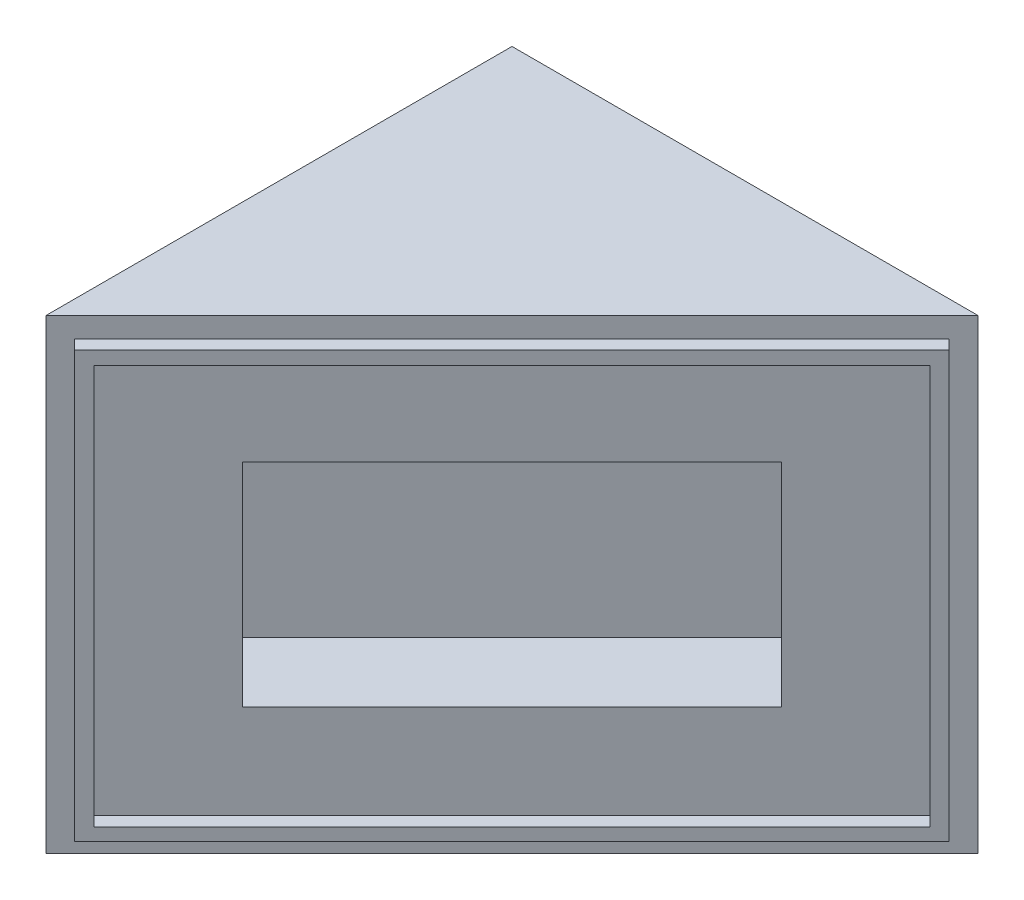
SolidWorks part; units mm, degrees
ref_plane "Front Plane" through (0, 0, 0) normal (0, 0, 1) x (1, 0, 0)
ref_plane "Top Plane" through (0, 0, 0) normal (0, 1, 0) x (1, 0, 0)
ref_plane "Right Plane" through (0, 0, 0) normal (1, 0, 0) x (0, 0, -1)
sketch "Sketch1" plane through (0, 0, 0) normal (0, 1, 0) x (1, 0, 0)
  line L1 (0, 0) -> (69.85, 0)
  line L2 (0, 0) -> (0, 69.85)
  line L3 (0, 69.85) -> (69.85, 69.85)
  line L4 (69.85, 0) -> (69.85, 69.85)
  dimension "D1" = 69.85
  dimension "D2" = 69.85
extrude "Boss-Extrude1" add sketch "Sketch1" along normal blind 69.85
ref_plane "Plane1" through (0, 0, 0) normal (0.7071, 0, 0.7071) x (0.7071, 0, -0.7071)
sketch "Sketch2" plane through (0, 0, 0) normal (0.7071, 0, 0.7071) x (0.7071, 0, -0.7071)
  line L0 (98.7828, 69.85) -> (98.7828, 0) construction
  line L1 (98.7828, 0) -> (49.3914, 0) construction
  line L2 (49.3914, 0) -> (0, 0) construction
  line L3 (0, 69.85) -> (0, 0) construction
  line L4 (49.3914, 69.85) -> (0, 69.85) construction
  line L5 (98.7828, 69.85) -> (49.3914, 69.85) construction
  line L6 (98.7828, 69.85) -> (98.7828, 0)
  line L7 (98.7828, 0) -> (49.3914, 0)
  line L8 (49.3914, 0) -> (0, 0)
  line L9 (0, 69.85) -> (0, 0)
  line L10 (49.3914, 69.85) -> (0, 69.85)
  line L11 (98.7828, 69.85) -> (49.3914, 69.85)
extrude "Cut-Extrude2" cut sketch "Sketch2" along normal blind 100
sketch "Sketch3" plane through (0, 0, 0) normal (0.7071, 0, 0.7071) x (0.7071, 0, -0.7071)
  line L0 (98.7828, 69.85) -> (98.7828, 0) construction
  line L1 (5.074, 34.8406) -> (93.7028, 34.8406) construction
  line L2 (49.3884, 64.77) -> (49.3884, 4.9111) construction
  line L3 (98.7828, 69.85) -> (0, 69.85) construction
  line L16 (95.7348, 66.802) -> (3, 66.802)
  line L17 (3, 66.802) -> (3, 3)
  line L18 (3, 3) -> (95.7348, 3)
  line L19 (95.7348, 3) -> (95.7348, 66.802)
  line L24 (93.7028, 64.77) -> (5.074, 64.77)
  line L25 (5.074, 64.77) -> (5.074, 4.9111)
  line L26 (5.074, 4.9111) -> (93.7028, 4.9111)
  line L27 (93.7028, 4.9111) -> (93.7028, 64.77)
  dimension "D1" = 3.048
  dimension "D2" = 3.048
  dimension "D3" = 2.032
  dimension "D4" = 2.032
extrude "Boss-Extrude2" add sketch "Sketch3" along normal blind 2.032
sketch "Sketch4" plane through (0, 0, 0) normal (0.7071, 0, 0.7071) x (0.7071, 0, -0.7071)
  line L0 (0, 69.85) -> (98.7828, 0) construction
  line L2 (98.7828, 69.85) -> (0, 0) construction
  line L4 (20.8164, 19.05) -> (77.9664, 19.05)
  line L5 (20.8164, 19.05) -> (20.8164, 50.8)
  line L6 (20.8164, 50.8) -> (77.9664, 50.8)
  line L7 (77.9664, 19.05) -> (77.9664, 50.8)
  line L8 (20.8164, 19.05) -> (77.9664, 50.8) construction
  line L9 (20.8164, 50.8) -> (77.9664, 19.05) construction
  point P4 (49.3914, 34.925)
  dimension "D1" = 57.15
  dimension "D2" = 31.75
extrude "Cut-Extrude3" cut sketch "Sketch4" against normal blind 12.7
